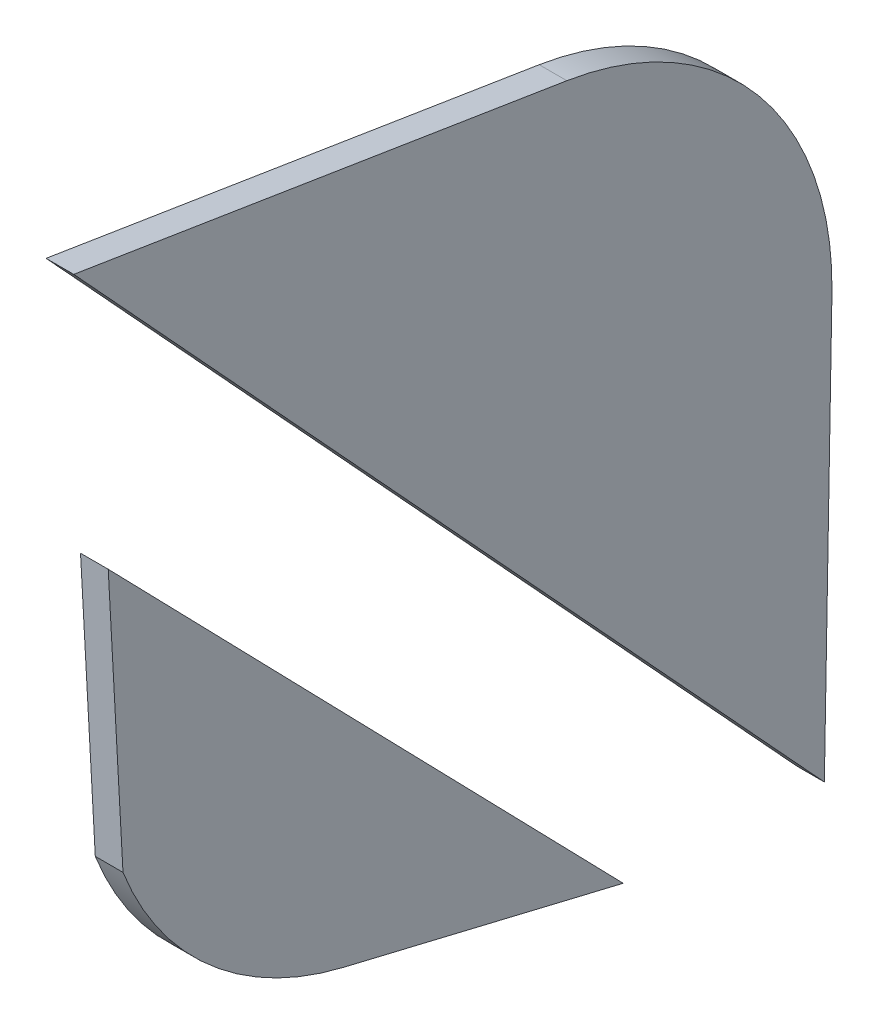
SolidWorks part; units mm, degrees
ref_plane "Alzado" through (0, 0, 0) normal (0, 0, 1) x (1, 0, 0)
ref_plane "Planta" through (0, 0, 0) normal (0, 1, 0) x (1, 0, 0)
ref_plane "Vista lateral" through (0, 0, 0) normal (1, 0, 0) x (0, 0, -1)
sketch "Croquis1" plane through (0, 0, 0) normal (1, 0, 0) x (0, 0, -1)
  line L0 (-38.7951, 76.8519) -> (14.6123, 68.3128)
  line L1 (43.3226, 34.0247) -> (42.5013, -11.4141)
  line L2 (-38.7951, 76.8519) -> (42.5013, -11.4141)
  line L3 (-33.4626, 18.0942) -> (-35.0622, 47.3278)
  line L4 (20.7155, -10.0207) -> (-9.6142, -2.7499)
  line L5 (-35.0622, 47.3278) -> (20.7155, -10.0207)
  arc A0 (43.3226, 34.0247) -> (14.6123, 68.3128) centre (9.2286, 34.641) ccw
  arc A1 (-33.4626, 18.0942) -> (-9.6142, -2.7499) centre (-1.6649, 30.4101) ccw
extrude "Saliente-Extruir1" add sketch "Croquis1" along normal blind 3
